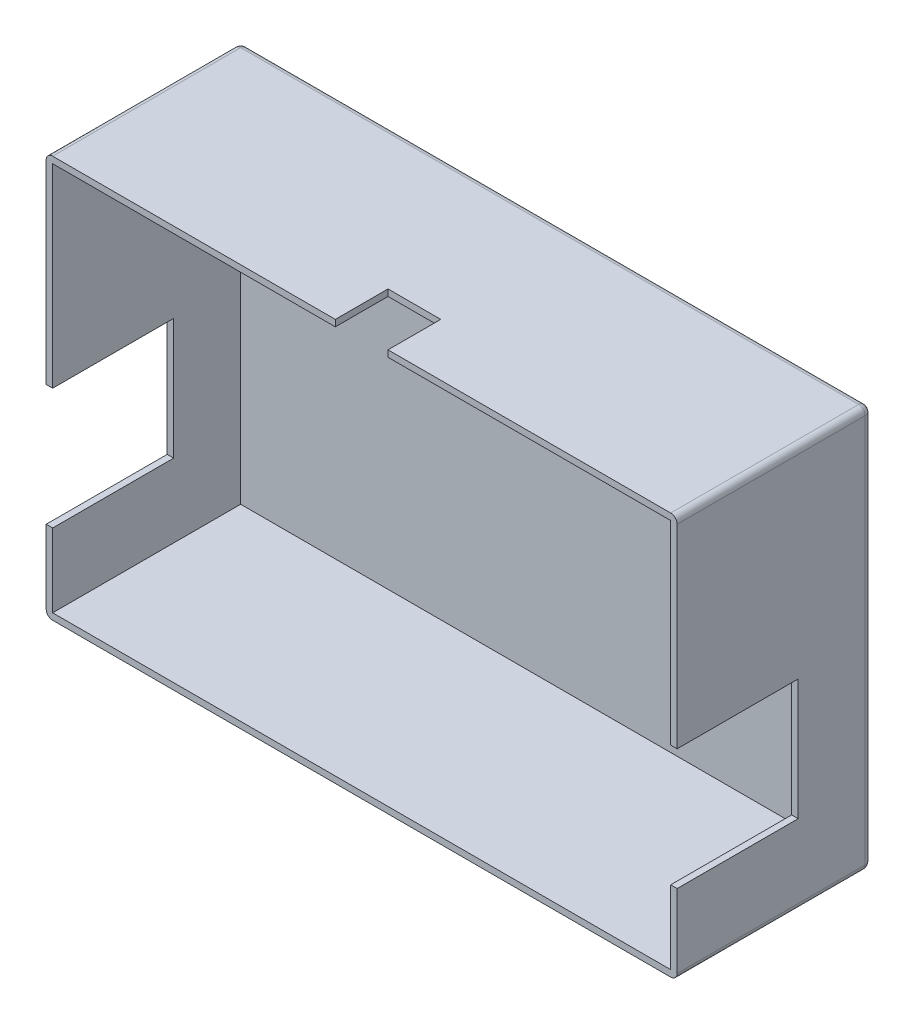
SolidWorks part; units mm, degrees
ref_plane "前视基准面" through (0, 0, 0) normal (0, 0, 1) x (1, 0, 0)
ref_plane "上视基准面" through (0, 0, 0) normal (0, 1, 0) x (1, 0, 0)
ref_plane "右视基准面" through (0, 0, 0) normal (1, 0, 0) x (0, 0, -1)
other "Configuration Table"
sketch "草图1" plane through (0, 0, 0) normal (0, 1, 0) x (1, 0, 0)
  line L1 (-73, -22.5) -> (73, -22.5)
  line L2 (-73, -22.5) -> (-73, 22.5)
  line L3 (-73, 22.5) -> (73, 22.5)
  line L4 (73, -22.5) -> (73, 22.5)
  line L5 (-73, -22.5) -> (73, 22.5) construction
  line L6 (-73, 22.5) -> (73, -22.5) construction
  point P0 (0, 0)
  dimension "D1" = 45
  dimension "D2" = 146
extrude "凸台-拉伸1" add sketch "草图1" along normal blind 93
sketch "草图2" plane through (-73, 0, 0) normal (-1, 0, 0) x (0, 0, 1)
  line L0 (22.5, 93) -> (-22.5, 0) construction
  line L4 (-22.5, 0) -> (22.5, 0)
  line L5 (22.5, 0) -> (22.5, 93)
  line L6 (22.5, 93) -> (-22.5, 93)
  line L7 (-22.5, 93) -> (-22.5, 0)
  line L9 (22.5, 0) -> (22.5, 93) construction
  line L10 (22.5, 93) -> (-22.5, 93) construction
  line L11 (-22.5, 93) -> (-22.5, 0) construction
  line L13 (-50.6416, 46.5) -> (-22.6416, 46.5) construction
  line L14 (-22.5, 0) -> (22.5, 0) construction
  line L15 (22.5, 46.5) -> (-5.5, 46.5)
  line L16 (-5.5, 46.5) -> (-5.5, 18.5)
  line L17 (-5.5, 18.5) -> (22.5, 18.5)
  line L18 (22.5, 18.5) -> (22.5, 46.5)
  dimension "D2" = 46.5
  dimension "D3" = 28
  dimension "D4" = 28
  dimension "D5" = 28
  dimension "D1" = 0
sketch "草图3" plane through (0, 93, 0) normal (0, 1, 0) x (1, 0, 0)
  line L0 (73, -22.5) -> (73, 22.5) construction
  line L1 (73, -22.5) -> (73, 22.5) construction
  line L2 (71.5, 1.5283) -> (71.5, -1.9849)
  dimension "D1" = 3
sketch "草图4" plane through (0, 93, 0) normal (0, 1, 0) x (1, 0, 0)
  line L0 (-6.1, -22.5) -> (6.1, -22.5)
  line L1 (-73, -22.5) -> (73, -22.5) construction
  line L2 (-6.1, -22.5) -> (-6.1, -10.3)
  line L3 (-6.1, -10.3) -> (6.1, -10.3)
  line L4 (6.1, -10.3) -> (6.1, -22.5)
  point P5 (0, -22.5)
  dimension "D1" = 12.2
  dimension "D2" = 12.2
shell "抽壳1" thickness 1.5
extrude "切除-拉伸1" cut sketch "草图2" against normal blind 1.5
extrude "切除-拉伸2" cut sketch "草图4" against normal blind 1.5
mirror "镜向1" about plane through (0, 0, 0) normal (1, 0, 0) of "切除-拉伸1"
fillet "圆角1" radius 1.5 8 edges at (73, 46.5, -22.5) (0, 93, -22.5) (-73, 46.5, -22.5) (0, 0, -22.5) (73, 93, 0) (-73, 0, 0) (-73, 93, 0) (73, 0, 0)
